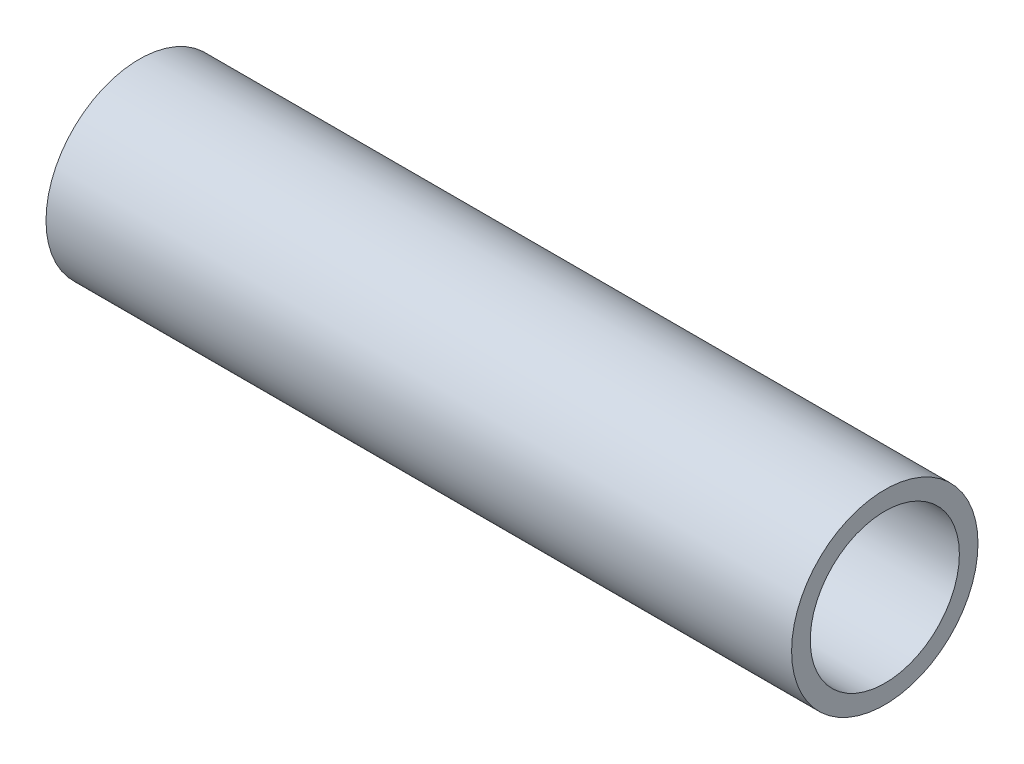
SolidWorks part; units mm, degrees
material "Hexcel AS4C (3000 丝)"
ref_plane "前视基准面" through (0, 0, 0) normal (0, 0, 1) x (1, 0, 0)
ref_plane "上视基准面" through (0, 0, 0) normal (0, 1, 0) x (1, 0, 0)
ref_plane "右视基准面" through (0, 0, 0) normal (1, 0, 0) x (0, 0, -1)
sketch "草图1" plane through (0, 0, 0) normal (1, 0, 0) x (0, 0, -1)
  circle A0 centre (0, 0) radius 4
  circle A1 centre (0, 0) radius 5
  dimension "D1" = 8
  dimension "D2" = 1
extrude "凸台-拉伸1" add sketch "草图1" along normal blind 40
